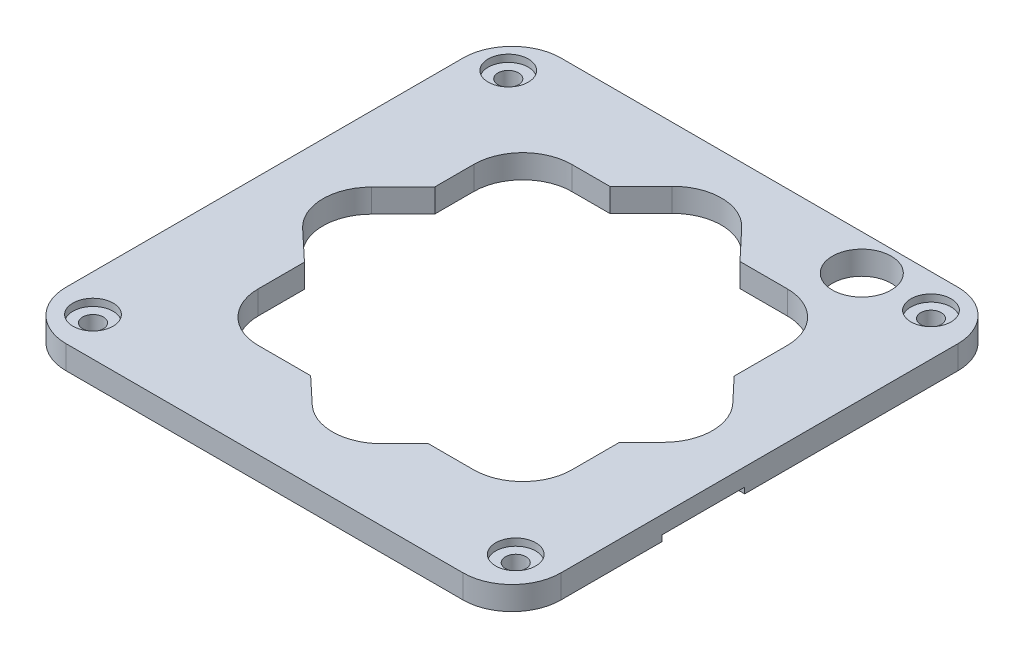
SolidWorks part; units mm, degrees
ref_plane "前视基准面" through (0, 0, 0) normal (0, 0, 1) x (1, 0, 0)
ref_plane "上视基准面" through (0, 0, 0) normal (0, 1, 0) x (1, 0, 0)
ref_plane "右视基准面" through (0, 0, 0) normal (1, 0, 0) x (0, 0, -1)
other "Configuration Table"
sketch "草图1" plane through (0, 0, 0) normal (0, 1, 0) x (1, 0, 0)
  line L1 (-20.25, 25.25) -> (20.25, 25.25)
  line L2 (-25.25, 20.25) -> (-25.25, -20.25)
  line L3 (-20.25, -25.25) -> (20.25, -25.25)
  line L4 (25.25, 20.25) -> (25.25, -20.25)
  line L5 (0, -25.25) -> (0, 25.25) construction
  line L6 (-25.25, 0) -> (25.25, 0) construction
  arc A0 (-20.25, -25.25) -> (-25.25, -20.25) centre (-20.25, -20.25) cw
  arc A1 (20.25, -25.25) -> (25.25, -20.25) centre (20.25, -20.25) ccw
  arc A2 (25.25, 20.25) -> (20.25, 25.25) centre (20.25, 20.25) ccw
  arc A3 (-20.25, 25.25) -> (-25.25, 20.25) centre (-20.25, 20.25) ccw
  point P0 (0, 0)
  point P8 (25.25, -25.25)
  point P11 (25.25, 25.25)
  point P15 (-25.25, 25.25)
  dimension "D3" = 5
  dimension "D1" = 50.5
  dimension "D2" = 50.5
extrude "凸台-拉伸1" add sketch "草图1" along normal blind 2.4
sketch "草图2" plane through (0, 2.4, 0) normal (0, 1, 0) x (1, 0, 0)
  circle A0 centre (21.3084, -20.9274) radius 1.05
  circle A1 centre (-21.4527, -21.3084) radius 1.05
  circle A2 centre (-21.8337, 21.4527) radius 1.05
  circle A3 centre (20.9274, 21.8337) radius 1.05
extrude "切除-拉伸1" cut sketch "草图2" against normal blind 10
sketch "草图3" plane through (0, 2.4, 0) normal (0, 1, 0) x (1, 0, 0)
  line L5 (-18.5157, 4.1837) -> (-15.3, 7.4274)
  line L6 (-18.3876, -2.9812) -> (-15.3, -5.8808)
  line L7 (4.702, -17.9643) -> (7.0274, -15.6)
  line L8 (3.9444, 19.4989) -> (6.8667, 16.4)
  line L9 (0, -16) -> (0, 16) construction
  line L10 (-16, 0) -> (16, 0) construction
  line L11 (-6.4051, 16.4) -> (-3.2441, 19.5886)
  line L12 (-10.3, 16.4) -> (-6.4051, 16.4)
  line L13 (-15.3, 11.4) -> (-15.3, 7.4274)
  line L14 (-10.3, -15.6) -> (-4.9508, -15.6)
  line L15 (16.7, 11.4) -> (16.7, 5.9726)
  line L16 (0, -16) -> (0, 16) construction
  line L17 (-16, 0) -> (16, 0) construction
  line L18 (6.8667, 16.4) -> (11.7, 16.4)
  line L19 (-4.9508, -15.6) -> (-2.2856, -18.103)
  line L20 (16.7, -5.7655) -> (18.9745, -3.453)
  line L21 (7.0274, -15.6) -> (11.7, -15.6)
  line L22 (16.7, -5.7655) -> (16.7, -10.6)
  line L23 (16.7, 5.9726) -> (19.0473, 3.4835)
  line L24 (-15.3, -5.8808) -> (-15.3, -10.6)
  arc A0 (-10.3, 16.4) -> (-15.3, 11.4) centre (-10.3, 11.4) ccw
  arc A1 (-18.5157, 4.1837) -> (-18.3876, -2.9812) centre (-14.9648, 0.6636) ccw
  arc A2 (-15.3, -10.6) -> (-10.3, -15.6) centre (-10.3, -10.6) ccw
  arc A3 (4.702, -17.9643) -> (-2.2856, -18.103) centre (1.1373, -14.4583) cw
  arc A4 (11.7, -15.6) -> (16.7, -10.6) centre (11.7, -10.6) ccw
  arc A5 (18.9745, -3.453) -> (19.0473, 3.4835) centre (15.4097, 0.0531) ccw
  arc A6 (16.7, 11.4) -> (11.7, 16.4) centre (11.7, 11.4) ccw
  arc A7 (3.9444, 19.4989) -> (-3.2441, 19.5886) centre (0.3068, 16.0685) ccw
  point P0 (0, 0)
  point P1 (0, 0)
  point P5 (0, 0)
  point P6 (22.5, -22.5)
  point P11 (22.5, 22.5)
  point P15 (-22.5, 22.5)
  point P22 (-15.3, 16.4)
  point P25 (-22.1323, 0.5355)
  point P32 (16.7, -15.6)
  point P35 (22.3511, -0.0199)
  point P38 (16.7, 16.4)
  point P42 (0.3966, 23.261)
  dimension "D3" = 32
  dimension "D5" = 5
  dimension "D1" = 32
  dimension "D2" = 32
  dimension "D4" = 32
extrude "切除-拉伸8" cut sketch "草图3" against normal through all
sketch "草图4" plane through (0, 2.4, 0) normal (0, 1, 0) x (1, 0, 0)
  circle A0 centre (-21.8337, 21.4527) radius 2.05
  circle A1 centre (20.9274, 21.8337) radius 2.05
  circle A2 centre (21.3084, -20.9274) radius 2.05
  circle A3 centre (-21.4527, -21.3084) radius 2.05
extrude "切除-拉伸9" cut sketch "草图4" against normal blind 0.73
sketch "草图5" plane through (0, 2.4, 0) normal (0, 1, 0) x (1, 0, 0)
  circle A0 centre (14.1074, 21.5906) radius 3
extrude "切除-拉伸10" cut sketch "草图5" against normal through all
sketch "草图6" plane through (0, 0, 0) normal (0, -1, 0) x (1, 0, 0)
  line L0 (26.0714, 9.7354) -> (26.0714, 1.7154) construction
  line L1 (39.6885, 9.948) -> (12.4543, 9.948)
  line L2 (39.6885, 9.948) -> (39.6885, 1.5027)
  line L3 (39.6885, 1.5027) -> (12.4543, 1.5027)
  line L4 (12.4543, 9.948) -> (12.4543, 1.5027)
  line L5 (26.0714, 1.5027) -> (26.0714, 9.948) construction
  line L6 (39.6885, 5.7254) -> (12.4543, 5.7254) construction
  arc A0 (13.7613, 1.4904) -> (11.4622, 0.6517) centre (13.0914, -0.2436) ccw construction
  point P0 (26.0714, 5.7254)
extrude "切除-拉伸12" cut sketch "草图6" against normal blind 0.6
